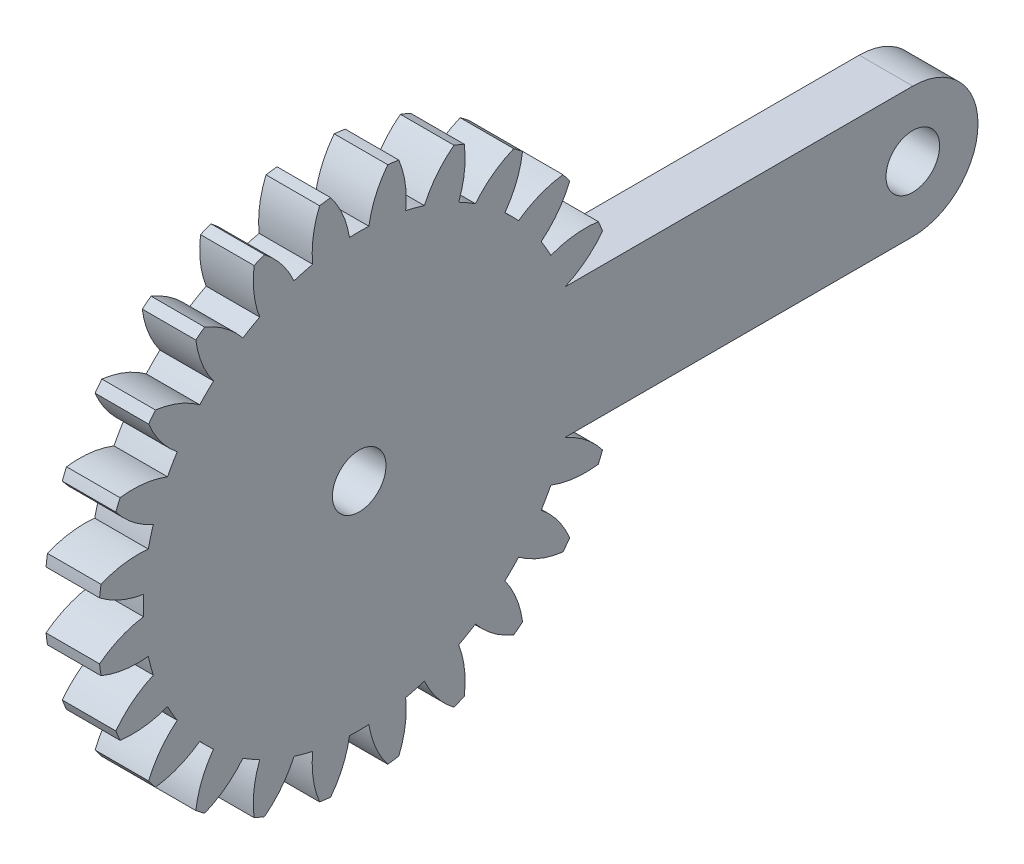
SolidWorks part; units mm, degrees
material "1060 Alloy"
ref_plane "Plane1" through (0, 0, 0) normal (0, 0, 1) x (1, 0, 0)
ref_plane "Plane2" through (0, 0, 0) normal (0, 1, 0) x (1, 0, 0)
ref_plane "Plane3" through (0, 0, 0) normal (1, 0, 0) x (0, 0, -1)
sketch "HoldingSke" plane through (0, 0, 0) normal (0, 1, 0) x (1, 0, 0)
  line L0 (0, 0) -> (0.812, -0.3615)
  line L1 (-15, 0) -> (100, 0) construction
  line L2 (0, 0) -> (-2.1039, 2.3779)
  line L3 (0, 0) -> (-11.863, 4.5341)
  line L4 (0, 0) -> (7.8894, 3.5126)
  line L5 (0, 0) -> (-46.8476, -17.4728)
  line L6 (0, 0) -> (-2.4869, -1.6779)
  line L7 (-2.1039, 2.3779) -> (8.6586, 51.2059)
  line L8 (-76.2, 54.61) -> (-76, 54.61)
  line L9 (-71.009, 38.7566) -> (-53.1078, 45.2721)
  line L10 (-76.2, 71.12) -> (104.1128, 71.12)
  line L11 (0, 0) -> (-3, 0)
  line L12 (-76.2, 101.6) -> (-76.158, 101.6)
  line L13 (24.9733, 27.94) -> (52.9518, 28.4284)
  line L14 (24.9733, 27.94) -> (24.9743, 27.94)
  line L15 (24.9733, 27.94) -> (100.4006, 29.5858)
  line L16 (-63.627, -1.125) -> (-12.827, -1.125)
  circle A0 centre (0, 0) radius 0.75
  circle A1 centre (0, 0) radius 12.0928
  circle A2 centre (0, 0) radius 37.5
  circle A3 centre (0, 0) radius 0.75
  dimension "MHD" = 24.1855
  dimension "Hub_dia" = 75
  dimension "Bore" = 1.5
  dimension "MBD" = 1.5
  dimension "Num_teeth" = 24
  dimension "Pitch_radius" = 180.3128
  dimension "Pitch" = 0.8889
  dimension "Width" = 3
  dimension "Overall_len" = 50
  dimension "Show_teeth" = 24
  dimension "Thickness" = 3
  dimension "OAL" = 50.0001
  dimension "T_dim" = 0.2
  dimension "Ap" = 20
  dimension "H" = 19.05
  dimension "Backlash" = 0.042
  dimension "Addendum_fac" = 1
  dimension "Dedendum_fac" = 1.25
  dimension "Clearance_fac" = 0.25
  dimension "Dedendum_add" = 0.001
  dimension "Module" = 1.125
sketch "BasProSke" plane through (0, 0, 0) normal (0, 1, 0) x (1, 0, 0)
  line L0 (-10, 0) -> (60, 0) construction
  line L1 (0, 0) -> (0, 14.625)
  line L2 (0, 0) -> (3, 0)
  line L3 (3, 0) -> (3, 14.625)
  line L4 (3, 14.625) -> (0, 14.625)
  dimension "Diameter" = 29.25
  dimension "Thickness" = 3
revolve "Base-Revolve" add sketch "BasProSke" angle 360 about L0
sketch "TooCutSke" plane through (0, 0, 0) normal (1, 0, 0) x (0, 0, -1)
  line L1 (0, 0) -> (0, 107) construction
  line L2 (0, 0) -> (-0.9564, 13.4661) construction
  line L3 (0, 0) -> (-3.5179, 26.7209) construction
  line L4 (-0.9564, 13.4661) -> (-1.7589, 13.3604) construction
  arc A0 (0.5427, 12.0806) -> (-0.5427, 12.0806) centre (0, 0) ccw
  arc A1 (1.6173, 14.5609) -> (-1.6173, 14.5609) centre (0, 0) ccw
  circle A2 centre (0, 0) radius 13.5 construction
  circle A3 centre (0, 0) radius 12.6859 construction
  arc A4 (-0.5427, 12.0806) -> (-1.6173, 14.5609) centre (-5.8773, 11.2423) ccw
  arc A5 (1.6173, 14.5609) -> (0.5427, 12.0806) centre (5.8773, 11.2423) ccw
  dimension "Root_dia" = 24.1855
  dimension "Overcut_dia" = 29.3008
  dimension "Pitch_dia" = 27
  dimension "Base_dia" = 25.3717
  dimension "Flank_rad" = 5.4
  dimension "Half_ang" = 7.5
  dimension "Half_CT" = 0.8094
extrude "ToothCut" cut sketch "TooCutSke" along normal through all
fillet "Breaks" [suppressed] radius 0.0225
fillet "RootFillets" [suppressed] radius 0.2823
pattern_circular "TeethCuts" count 24 every 15 about axis through (-10, 0, 0) along (1, 0, 0) of "ToothCut", "RootFillets", "Breaks"
sketch "HubNeaOneSke" plane through (0, 0, 0) normal (-1, 0, 0) x (0, 0, 1)
  circle A0 centre (0, 0) radius 12.0928
  dimension "Diameter" = 24.1855
extrude "HubNearOne" [suppressed] add sketch "HubNeaOneSke" along normal blind 47.0001
sketch "HubNeaBotSke" plane through (0, 0, 0) normal (-1, 0, 0) x (0, 0, 1)
  circle A0 centre (0, 0) radius 12.0928
  dimension "Diameter" = 24.1855
extrude "HubNearBoth" [suppressed] add sketch "HubNeaBotSke" along normal blind 23.5
ref_plane "FarPln" through (3, 0, 0) normal (1, 0, 0) x (0, 0, -1)
sketch "HubFarSke" plane through (3, 0, 0) normal (1, 0, 0) x (0, 0, -1)
  circle A0 centre (0, 0) radius 12.0928
  dimension "Diameter" = 24.1855
extrude "HubFar" [suppressed] add sketch "HubFarSke" along normal blind 23.5
sketch "BorSke" plane through (0, 0, 0) normal (1, 0, 0) x (0, 0, -1)
  circle A0 centre (0, 0) radius 1.5
  dimension "Diameter" = 3
extrude "Bore" cut sketch "BorSke" along normal mid plane 100.0001
sketch "KeySke" plane through (0, 0, 0) normal (1, 0, 0) x (0, 0, -1)
  line L0 (-0.3, 0) -> (-0.3, 0.95)
  line L1 (-0.3, 0.95) -> (0.3, 0.95)
  line L2 (0.3, 0.95) -> (0.3, 0)
  line L3 (0, 0) -> (0, 34) construction
  line L4 (-0.3, 0) -> (0.3, 0)
  dimension "Offset" = 0.95
  dimension "Width" = 0.6
extrude "Keyway" [suppressed] cut sketch "KeySke" along normal mid plane 100.0001
pattern_circular "Keyway2" [suppressed] count 2 every 90 about axis through (-10, 0, 0) along (1, 0, 0)
sketch "Sketch1" plane through (0, 0, 0) normal (1, 0, 0) x (0, 0, -1)
  line L0 (31, 3.6509) -> (11.5285, 3.6509)
  line L1 (11.5285, -3.6509) -> (31, -3.6509)
  line L3 (11.5285, -3.6509) -> (11.5285, 3.6509)
  arc A0 (31, -3.6509) -> (31, 3.6509) centre (31, 0) ccw
  circle A1 centre (31, 0) radius 1.5
  point P6 (0, 0)
  dimension "D2" = 3
  dimension "D3" = 3.6509
  dimension "D1" = 31
extrude "Boss-Extrude1" add sketch "Sketch1" along normal blind 3
equation "' \"Module@HoldingSke\" = 6.35"
equation "' \"Num_teeth@HoldingSke\" = 12"
equation "' \"Ap@HoldingSke\" =  20"
equation "' \"Width@HoldingSke\" = 0.5 * 25.4"
equation "' \"Hub_dia@HoldingSke\"= 1 * 25.4"
equation "' \"Overall_len@HoldingSke\" = 1.0 * 25.4"
equation "' \"Bore@HoldingSke\" = 0.75 * 25.4"
equation "' \"T_dim@HoldingSke\" = 0.1 * 25.4"
equation "' \"Width@KeySke\" = 0.25 * 25.4"
equation "' \"Show_teeth@HoldingSke\" = 13"
equation "' \"Backlash@HoldingSke\" = 0.009 * 25.4"
equation "' \"Addendum_fac@HoldingSke\" = 1.0"
equation "' \"Dedendum_fac@HoldingSke\" = 1.25"
equation "' \"Dedendum_add@HoldingSke\" = 0.00005 * 25.4"
equation "' \"Clearance_fac@HoldingSke\" = 0.25"
equation "\"Pitch@HoldingSke\" = 1 / \"Module@HoldingSke\""
equation "\"Overcut_dia@TooCutSke\" = (\"Num_teeth@HoldingSke\" + 2 * \"Addendum_fac@HoldingSke\") / \"Pitch@HoldingSke\" + 0.002 * 25.4"
equation "\"Pitch_dia@TooCutSke\" = \"Num_teeth@HoldingSke\" / \"Pitch@HoldingSke\""
equation "\"Base_dia@TooCutSke\" = \"Num_teeth@HoldingSke\" / \"Pitch@HoldingSke\" * cos((\"Ap@HoldingSke\"  * 3.14159265 / 180))"
equation "\"Root_dia@TooCutSke\" = (\"Num_teeth@HoldingSke\" + 2) / \"Pitch@HoldingSke\" - 2 * (\"Addendum_fac@HoldingSke\" + \"Dedendum_fac@HoldingSke\") / \"Pitch@HoldingSke\" - \"Dedendum_add@HoldingSke\" * 2"
equation "\"Half_ang@TooCutSke\" = 180 / \"Num_teeth@HoldingSke\""
equation "\"Half_CT@TooCutSke\" = \"Num_teeth@HoldingSke\" / \"Pitch@HoldingSke\" * sin((3.14159265 / 2 / \"Num_teeth@HoldingSke\")) / 2 - 7 * \"Backlash@HoldingSke\" / 4"
equation "\"Flank_rad@TooCutSke\" = \"Num_teeth@HoldingSke\" / \"Pitch@HoldingSke\" / 5"
equation "\"Radius@RootFillets\" = \"Clearance_fac@HoldingSke\" / \"Pitch@HoldingSke\" + \"Dedendum_add@HoldingSke\""
equation "\"Break_rad@Breaks\" = 0.02 / \"Pitch@HoldingSke\""
equation "\"Thickness@HoldingSke\" = \"Width@HoldingSke\""
equation "\"OAL@HoldingSke\" = \"Thickness@HoldingSke\""
equation "\"MHD@HoldingSke\" = (\"Num_teeth@HoldingSke\" + 2) / \"Pitch@HoldingSke\" - 2 * (\"Addendum_fac@HoldingSke\" + \"Dedendum_fac@HoldingSke\")  / \"Pitch@HoldingSke\" - \"Dedendum_add@HoldingSke\" * 2"
equation "\"MBD@HoldingSke\" = (\"Num_teeth@HoldingSke\" + 2) / \"Pitch@HoldingSke\" - 2 * (\"Addendum_fac@HoldingSke\" + \"Dedendum_fac@HoldingSke\")  / \"Pitch@HoldingSke\" - \"Dedendum_add@HoldingSke\" * 2 - 0.002 * 25.4"
equation "\"MHD@HoldingSke\" = ((sgn( \"MHD@HoldingSke\" - \"Hub_dia@HoldingSke\" )-1)*( \"MHD@HoldingSke\" - \"Hub_dia@HoldingSke\" ))/-2+ \"Hub_dia@HoldingSke\""
equation "\"MBD@HoldingSke\" = ((sgn( \"MBD@HoldingSke\" - \"Bore@HoldingSke\" )-1)*( \"MBD@HoldingSke\" - \"Bore@HoldingSke\" ))/-2+ \"Bore@HoldingSke\""
equation "\"OAL@HoldingSke\" = ((sgn( \"OAL@HoldingSke\" - \"Overall_len@HoldingSke\" )+1)*( \"OAL@HoldingSke\" - \"Overall_len@HoldingSke\" ))/2 + \"Overall_len@HoldingSke\" + 0.000002 * 25.4"
equation "\"Num_teeth@TeethCuts\" = int( \"Show_teeth@HoldingSke\" ) + 1"
equation "\"Num_teeth@TeethCuts\" = ((sgn( \"Num_teeth@TeethCuts\" - \"Num_teeth@HoldingSke\" )-1)*( \"Num_teeth@TeethCuts\" - \"Num_teeth@HoldingSke\" ))/-2+ \"Num_teeth@HoldingSke\""
equation "\"Num_teeth@TeethCuts\" = ((sgn( \"Num_teeth@TeethCuts\" - 2.0)+1)*( \"Num_teeth@TeethCuts\" - 2.0))/2 +2.0"
equation "\"Angle@TeethCuts\" = 360.0 / \"Num_teeth@HoldingSke\""
equation "\"Diameter@BasProSke\" = (\"Num_teeth@HoldingSke\" + 2 * \"Addendum_fac@HoldingSke\") / \"Pitch@HoldingSke\""
equation "\"Thickness@BasProSke\"  = \"Thickness@HoldingSke\""
equation "' \"Fillet_rad@BasProSke\" =  \"Thickness@HoldingSke\" * 0.05"
equation "\"MHD@HoldingSke\" = ((sgn( \"MHD@HoldingSke\" - \"Root_dia@TooCutSke\" )-1)*( \"MHD@HoldingSke\" - \"Root_dia@TooCutSke\" ))/-2+ \"Root_dia@TooCutSke\""
equation "\"Diameter@HubNeaOneSke\" = \"MHD@HoldingSke\""
equation "\"Length@HubNearOne\" = \"OAL@HoldingSke\" - \"Thickness@BasProSke\""
equation "\"Diameter@HubNeaBotSke\" = \"MHD@HoldingSke\""
equation "\"Length@HubNearBoth\" = ( \"OAL@HoldingSke\" - \"Thickness@BasProSke\" ) / 2.0"
equation "\"Thickness@FarPln\" = \"Thickness@BasProSke\""
equation "\"Diameter@HubFarSke\" = \"MHD@HoldingSke\""
equation "\"Length@HubFar\" = ( \"OAL@HoldingSke\" - \"Thickness@BasProSke\" ) / 2.0"
equation "\"D1@Bore\" = \"OAL@HoldingSke\" * 2.0"
equation "\"D1@Keyway\" = \"OAL@HoldingSke\" * 2.0"
equation "\"Offset@KeySke\" = \"T_dim@HoldingSke\" + \"MBD@HoldingSke\" / 2.0"
